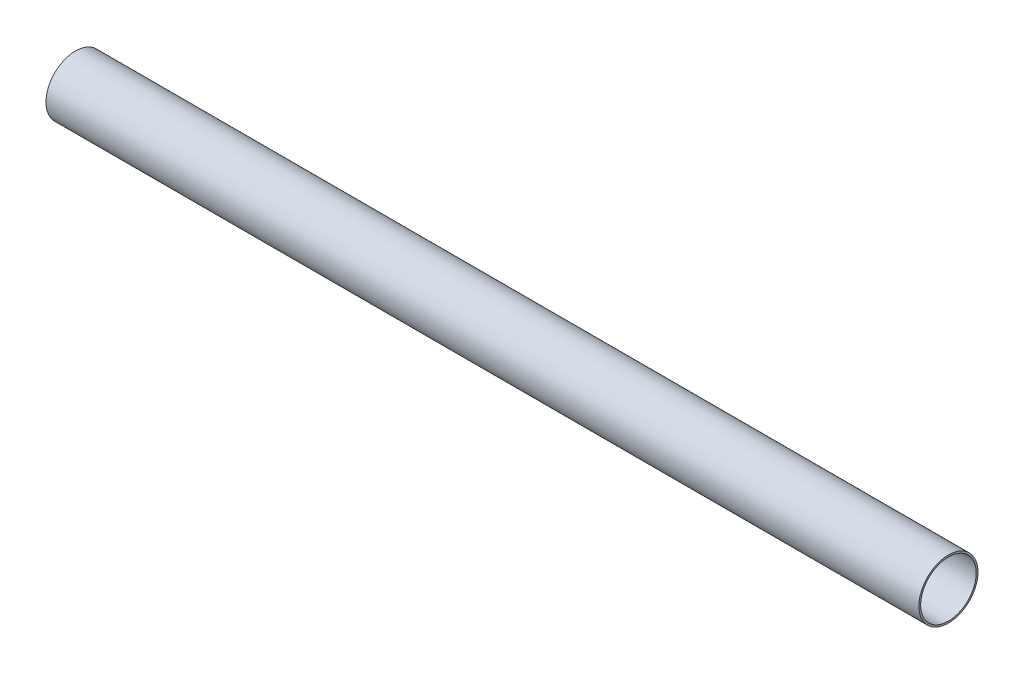
SolidWorks part; units mm, degrees
ref_plane "Front" through (0, 0, 0) normal (0, 0, 1) x (1, 0, 0)
ref_plane "Top" through (0, 0, 0) normal (0, 1, 0) x (1, 0, 0)
ref_plane "Right" through (0, 0, 0) normal (1, 0, 0) x (0, 0, -1)
sketch "Sketch1" plane through (0, 0, 0) normal (1, 0, 0) x (0, 0, -1)
  circle A0 centre (0, 0) radius 20.6375
  circle A1 centre (0, 0) radius 19.3929
  point P4 (20.6375, 0)
  point P5 (19.3929, 0)
  dimension "OD" = 41.275
  dimension "ID" = 38.7858
  dimension "Wall" = 1.2446
extrude "Extrude1" add sketch "Sketch1" along normal mid plane 609.6
sketch "Sketch2" plane through (0, 0, 0) normal (0, 0, 1) x (1, 0, 0)
  line L0 (-304.8, 0) -> (304.8, 0) construction
  line L1 (-304.8, 20.6375) -> (-304.8, -20.6375) construction
